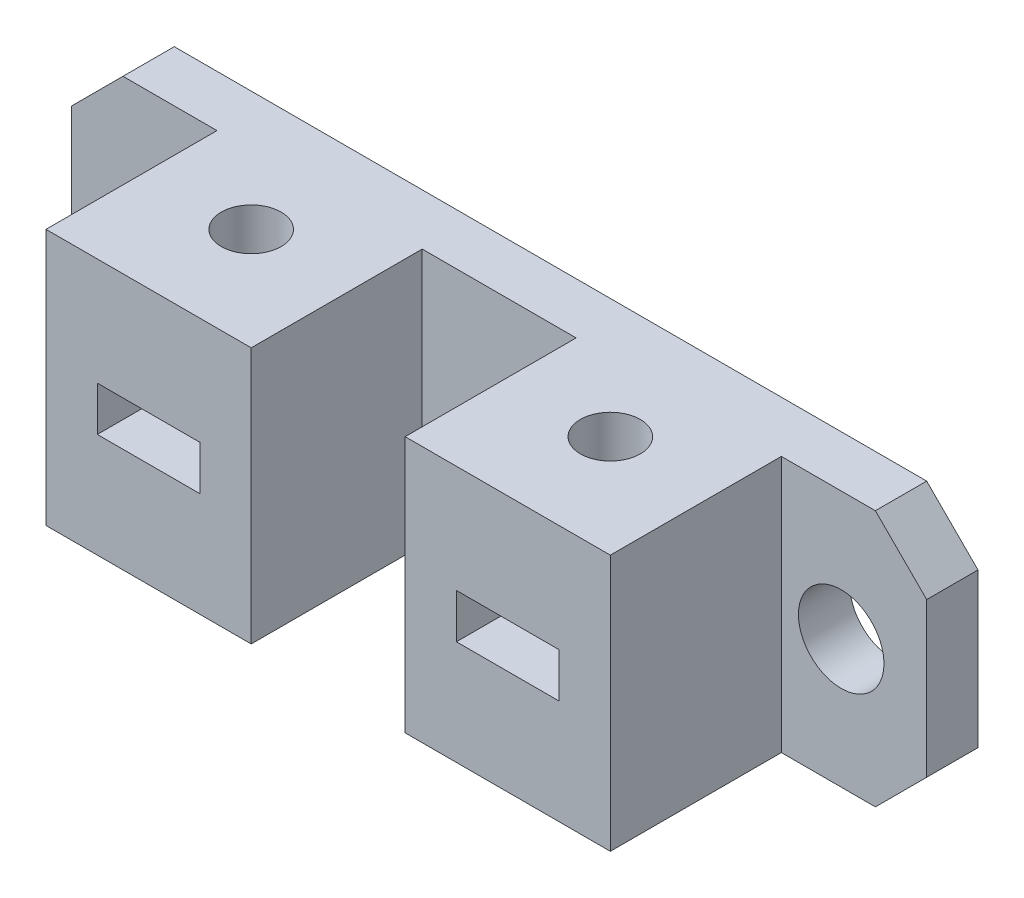
SolidWorks part; units mm, degrees
ref_plane "Front Plane" through (0, 0, 0) normal (0, 0, 1) x (1, 0, 0)
ref_plane "Top Plane" through (0, 0, 0) normal (0, 1, 0) x (1, 0, 0)
ref_plane "Right Plane" through (0, 0, 0) normal (1, 0, 0) x (0, 0, -1)
sketch "Sketch1" plane through (0, 0, 0) normal (0, 0, 1) x (1, 0, 0)
  line L1 (0, 0) -> (50, 0)
  line L2 (0, 0) -> (0, 15)
  line L3 (0, 15) -> (50, 15)
  line L4 (50, 0) -> (50, 15)
  dimension "D1" = 15
  dimension "D2" = 50
extrude "Boss-Extrude1" add sketch "Sketch1" along normal blind 3
sketch "Sketch2" plane through (0, 0, 3) normal (0, 0, 1) x (1, 0, 0)
  line L0 (50, 15) -> (0, 15) construction
  line L1 (0, 15) -> (0, 0) construction
  line L2 (25, 15) -> (25, -2.3877) construction
  circle A0 centre (5, 7.5) radius 2.5
  circle A1 centre (45, 7.5) radius 2.5
  dimension "D1" = 7.5
  dimension "D2" = 5
extrude "Cut-Extrude1" cut sketch "Sketch2" against normal through all
sketch "Sketch3" plane through (0, 0, 3) normal (0, 0, 1) x (1, 0, 0)
  line L0 (50, 15) -> (0, 15) construction
  line L1 (8.5, 15) -> (20.5, 15)
  line L2 (8.5, 15) -> (8.5, 0)
  line L3 (8.5, 0) -> (20.5, 0)
  line L4 (20.5, 15) -> (20.5, 0)
  line L5 (0, 0) -> (50, 0) construction
  line L6 (25, 15) -> (25, -4.6241) construction
  line L7 (11.5, 8.7126) -> (17.5, 8.7126)
  line L8 (11.5, 8.7126) -> (11.5, 6.1126)
  line L9 (11.5, 6.1126) -> (17.5, 6.1126)
  line L10 (17.5, 8.7126) -> (17.5, 6.1126)
  line L11 (32.5, 8.7126) -> (32.5, 6.1126)
  line L12 (38.5, 6.1126) -> (32.5, 6.1126)
  line L13 (38.5, 8.7126) -> (38.5, 6.1126)
  line L14 (38.5, 8.7126) -> (32.5, 8.7126)
  line L15 (29.5, 15) -> (29.5, 0)
  line L16 (41.5, 0) -> (29.5, 0)
  line L17 (41.5, 15) -> (41.5, 0)
  line L18 (41.5, 15) -> (29.5, 15)
  line L19 (0, 15) -> (0, 0) construction
  dimension "D1" = 12
  dimension "D2" = 6
  dimension "D3" = 2.6
  dimension "D4" = 3
  dimension "D5" = 8.5
extrude "Boss-Extrude2" add sketch "Sketch3" along normal blind 10
sketch "Sketch4" plane through (0, 15, 0) normal (0, 1, 0) x (1, 0, 0)
  line L0 (50, 0) -> (0, 0) construction
  line L1 (41.5, -13) -> (41.5, -3) construction
  line L2 (25, 0) -> (25, -13.6549) construction
  circle A0 centre (35.5, -7) radius 1.75
  circle A1 centre (14.5, -7) radius 1.75
  dimension "D1" = 7
  dimension "D2" = 6
  dimension "D3" = 6
  dimension "D4" = 3.5
extrude "Cut-Extrude2" cut sketch "Sketch4" against normal through all
chamfer "Chamfer1" distance 3 angle 45 4 edges at (50, 15, 1.5) (50, 0, 1.5) (0, 0, 1.5) (0, 15, 1.5)
